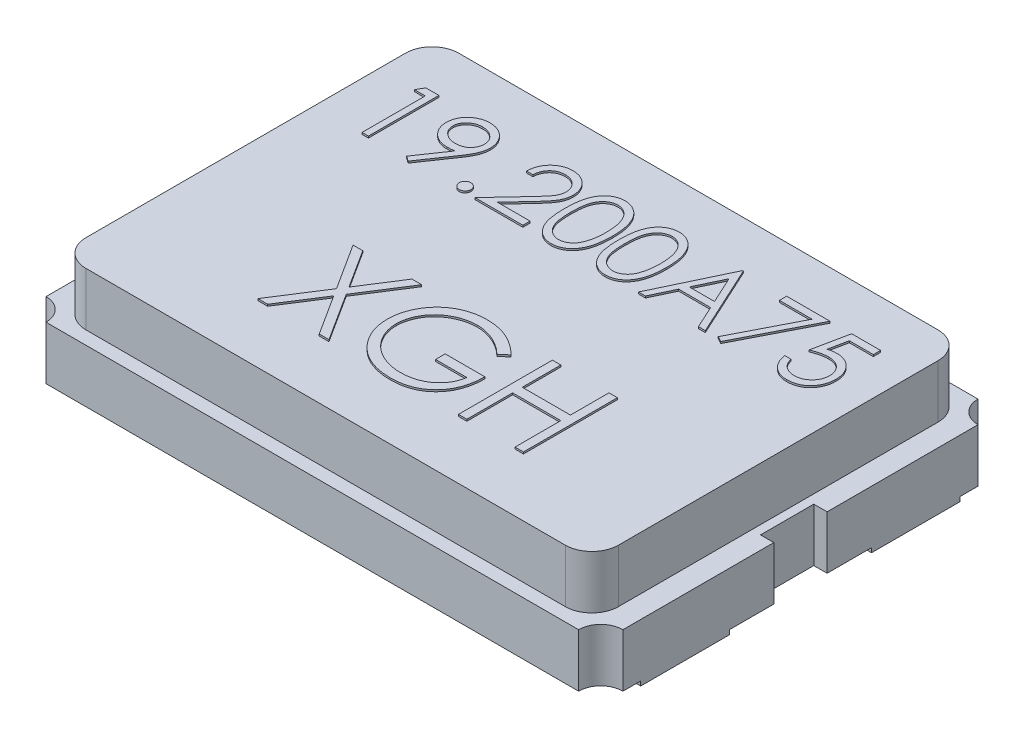
SolidWorks part; units mm, degrees
ref_plane "Plano frontal" through (0, 0, 0) normal (0, 0, 1) x (1, 0, 0)
ref_plane "Plano superior" through (0, 0, 0) normal (0, 1, 0) x (1, 0, 0)
ref_plane "Plano direito" through (0, 0, 0) normal (1, 0, 0) x (0, 0, -1)
sketch "Sketch1" plane through (0, 0, 0) normal (0, 1, 0) x (1, 0, 0)
  line L0 (-3.25, 2) -> (-3.25, 0.3)
  line L5 (-3.25, 0.3) -> (-3.1, 0.3)
  line L7 (-3.25, -0.3) -> (-3.1, -0.3)
  line L8 (-3.1, 0.3) -> (-3.1, -0.3)
  line L9 (3.25, 0.3) -> (3.1, 0.3)
  line L11 (3.25, -0.3) -> (3.1, -0.3)
  line L12 (3.1, 0.3) -> (3.1, -0.3)
  line L13 (-3.25, -0.3) -> (-3.25, -2)
  line L14 (-3, -2.25) -> (3, -2.25)
  line L15 (3.25, -2) -> (3.25, -0.3)
  line L16 (3.25, 0.3) -> (3.25, 2)
  line L17 (3, 2.25) -> (-3, 2.25)
  arc A0 (-3.25, 2) -> (-3, 2.25) centre (-3.25, 2.25) ccw
  arc A1 (-3, -2.25) -> (-3.25, -2) centre (-3.25, -2.25) ccw
  arc A2 (3.25, -2) -> (3, -2.25) centre (3.25, -2.25) ccw
  arc A3 (3, 2.25) -> (3.25, 2) centre (3.25, 2.25) ccw
  dimension "D5" = 0.25
  dimension "D6" = 0.25
  dimension "D7" = 0.25
  dimension "D8" = 0.25
  dimension "D2" = 1.7
  dimension "D3" = 1.7
  dimension "D4" = 1.7
  dimension "D9" = 0.6
  dimension "D10" = 0.3
  dimension "D11" = 0.15
  dimension "D12" = 0.15
  dimension "D13" = 0.6
  dimension "D14" = 6
  dimension "D15" = 6
  dimension "D16" = 3
  dimension "D17" = 0.25
  dimension "D18" = 0.25
  dimension "D19" = 0.25
  dimension "D20" = 0.25
extrude "Extrude1" add sketch "Sketch1" along normal blind 0.6
sketch "Sketch2" plane through (0, 0.6, 0) normal (0, 1, 0) x (1, 0, 0)
  line L1 (-2.7, 2.1) -> (2.7, 2.1)
  line L2 (-3, 1.8) -> (-3, -1.8)
  line L3 (-2.7, -2.1) -> (2.7, -2.1)
  line L4 (3, 1.8) -> (3, -1.8)
  arc A0 (3.25, -2) -> (3, -2.25) centre (3.25, -2.25) ccw construction
  arc A1 (-2.7, 2.1) -> (-3, 1.8) centre (-2.7, 1.8) ccw
  arc A2 (2.7, 2.1) -> (3, 1.8) centre (2.7, 1.8) cw
  arc A3 (2.7, -2.1) -> (3, -1.8) centre (2.7, -1.8) ccw
  arc A4 (-3, -1.8) -> (-2.7, -2.1) centre (-2.7, -1.8) ccw
  point P10 (-3, 2.1)
  point P13 (3, 2.1)
  point P16 (3.0128, -2.1709)
  point P19 (-2.8, -3.1)
  dimension "D4" = 0.3
  dimension "D1" = 3
  dimension "D2" = 6
  dimension "D3" = 2.1
  dimension "D5" = 2.1
extrude "Extrude2" add sketch "Sketch2" along normal blind 0.6
sketch "Sketch3" plane through (0, 0, 0) normal (0, -1, 0) x (1, 0, 0)
  line L1 (-3.25, 0.3) -> (-3.25, 2) construction
  line L2 (-3.25, 1.8) -> (-2.25, 1.8)
  line L3 (-3.25, 1.8) -> (-3.25, 0.8)
  line L4 (-3.25, 0.8) -> (-2.25, 0.8)
  line L6 (-2.25, 1.8) -> (-2.25, 0.8)
  line L7 (-3.25, -2) -> (-3.25, -0.3) construction
  line L8 (-3.25, -1.8) -> (-2.25, -1.8)
  line L9 (-3.25, -1.8) -> (-3.25, -0.8)
  line L10 (-3.25, -0.8) -> (-2.25, -0.8)
  line L11 (-2.25, -1.8) -> (-2.25, -0.8)
  line L12 (3.25, 2) -> (3.25, 0.3) construction
  line L13 (3.25, 1.8) -> (2.25, 1.8)
  line L14 (3.25, 1.8) -> (3.25, 0.8)
  line L15 (3.25, 0.8) -> (2.25, 0.8)
  line L16 (2.25, 1.8) -> (2.25, 0.8)
  line L17 (3.25, -0.3) -> (3.25, -2) construction
  line L18 (3.25, -0.8) -> (2.25, -0.8)
  line L19 (3.25, -0.8) -> (3.25, -1.8)
  line L20 (3.25, -1.8) -> (2.25, -1.8)
  line L21 (2.25, -0.8) -> (2.25, -1.8)
  dimension "D1" = 1
  dimension "D2" = 1
  dimension "D3" = 1
  dimension "D4" = 1
  dimension "D5" = 1
  dimension "D6" = 1
  dimension "D7" = 1
  dimension "D8" = 1
  dimension "D9" = 0.8
  dimension "D10" = 0.8
  dimension "D11" = 0.8
  dimension "D12" = 0.8
extrude "Extrude3" add sketch "Sketch3" along normal blind 0.05
sketch "Sketch4" plane through (0, 1.2, 0) normal (0, 1, 0) x (1, 0, 0)
  text T0 "19.200A75" font "Century Gothic" height in points 3
extrude "Extrude4" add sketch "Sketch4" along normal blind 0.02
sketch "Sketch5" plane through (0, 1.2, 0) normal (0, 1, 0) x (1, 0, 0)
  text T0 "XGH" font "Century Gothic" height in points 4
extrude "Extrude5" add sketch "Sketch5" along normal blind 0.02
